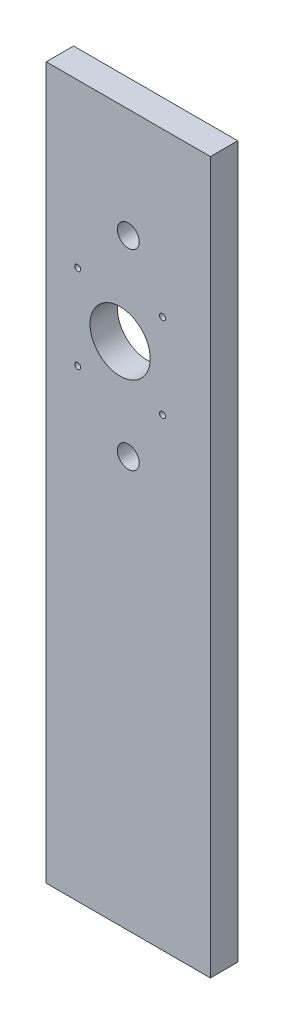
SolidWorks part; units mm, degrees
ref_plane "Alzado" through (0, 0, 0) normal (0, 0, 1) x (1, 0, 0)
ref_plane "Planta" through (0, 0, 0) normal (0, 1, 0) x (1, 0, 0)
ref_plane "Vista lateral" through (0, 0, 0) normal (1, 0, 0) x (0, 0, -1)
sketch "Croquis1" plane through (0, 0, 0) normal (0, 0, 1) x (1, 0, 0)
  line L0 (-30, 55) -> (30, 55) construction
  line L1 (-30, 130) -> (30, 130)
  line L2 (-30, 130) -> (-30, -130)
  line L3 (-30, -130) -> (30, -130)
  line L4 (30, 130) -> (30, -130)
  line L5 (-30, 130) -> (30, -130) construction
  line L6 (-30, -130) -> (30, 130) construction
  line L7 (0, 130) -> (0, -130) construction
  line L8 (-30, 20) -> (30, 20) construction
  line L9 (-30, 90) -> (30, 90) construction
  circle A0 centre (-3, 55) radius 11
  circle A1 centre (0, 90) radius 4
  circle A2 centre (0, 20) radius 4
  circle A3 centre (-18.5, 70.5) radius 1.09
  circle A4 centre (12.5, 70.5) radius 1.09
  circle A5 centre (12.5, 39.5) radius 1.09
  circle A6 centre (-18.5, 39.5) radius 1.09
  point P0 (0, 0)
  dimension "D4" = 22
  dimension "D7" = 8
  dimension "D8" = 8
  dimension "D10" = 2.18
  dimension "D11" = 2.18
  dimension "D12" = 2.18
  dimension "D13" = 2.18
  dimension "D1" = 60
  dimension "D2" = 260
  dimension "D3" = 75
  dimension "D9" = 3
  dimension "D5" = 35
  dimension "D6" = 35
extrude "Saliente-Extruir1" add sketch "Croquis1" along normal blind 10
